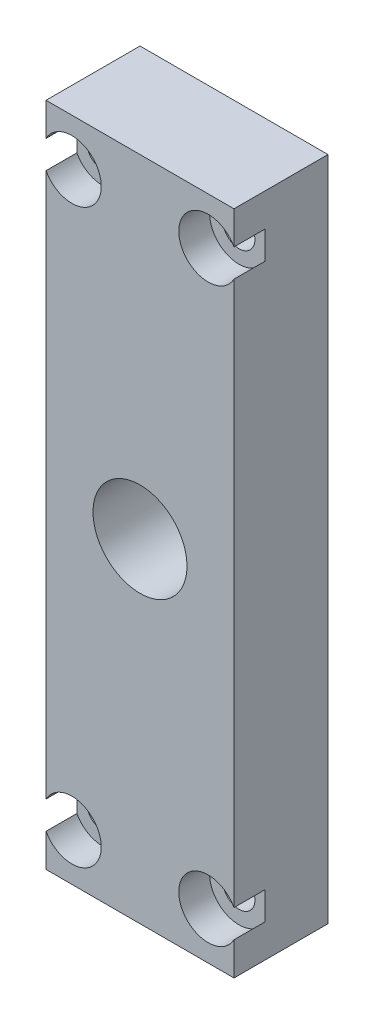
SolidWorks part; units mm, degrees
ref_plane "Front Plane" through (0, 0, 0) normal (0, 0, 1) x (1, 0, 0)
ref_plane "Top Plane" through (0, 0, 0) normal (0, 1, 0) x (1, 0, 0)
ref_plane "Right Plane" through (0, 0, 0) normal (1, 0, 0) x (0, 0, -1)
sketch "Sketch1" plane through (0, 0, 0) normal (0, 1, 0) x (1, 0, 0)
  line L1 (0, 0) -> (25.4, 0)
  line L2 (0, 0) -> (0, 12.7)
  line L3 (0, 12.7) -> (25.4, 12.7)
  line L4 (25.4, 0) -> (25.4, 12.7)
  dimension "D1" = 12.7
  dimension "D2" = 25.4
extrude "Boss-Extrude1" add sketch "Sketch1" along normal blind 90.0176
sketch "Sketch2" plane through (0, 0, 0) normal (0, 0, 1) x (1, 0, 0)
  line L0 (3.4925, 6.358) -> (21.9075, 6.358)
  line L1 (3.4925, 83.6676) -> (21.9075, 83.6676)
hole_wizard "CBORE for #8 Socket Head Cap Screw1" positions "3DSketch1" profile "Sketch4" counterbore size "#8" standard "ANSI Inch"
sketch3d "3DSketch1"
  point P0 (3.4925, 6.358, 0)
  point P3 (21.9075, 6.358, 0)
  point P6 (21.9075, 83.6676, 0)
  point P9 (3.4925, 83.6676, 0)
sketch "Sketch4" plane through (3.4925, 6.358, 0) normal (1, 0, 0) x (0, -1, 0)
  line L0 (0, 0) -> (0, 20.3434)
  line L1 (0, 20.3434) -> (2.1526, 19.05)
  line L2 (2.1526, 19.05) -> (2.1526, 4.1656)
  line L3 (2.1526, 4.1656) -> (3.9688, 4.1656)
  line L4 (3.9688, 4.1656) -> (3.9688, 0)
  line L5 (3.9688, 0) -> (0, 0)
  line L10 (0, 20.3434) -> (-2.1527, 19.05) construction
  line L11 (0, -6.35) -> (0, 107.95) construction
  dimension "Hole Dia." = 4.3053
  dimension "Hole Depth" = 19.05
  dimension "C'Bore Dia." = 7.9375
  dimension "C'Bore Depth" = 4.1656
  dimension "Drill Angle" = 118
sketch "Sketch5" plane through (0, 0, 0) normal (0, 0, 1) x (1, 0, 0)
  line L0 (12.7, 90.0176) -> (12.7, 0) construction
  line L1 (0, 90.0176) -> (25.4, 90.0176) construction
  line L2 (0, 0) -> (25.4, 0) construction
  line L3 (0, 45.0128) -> (25.4, 45.0128) construction
  line L4 (0, 81.7825) -> (0, 8.243) construction
  line L5 (25.4, 81.7825) -> (25.4, 8.243) construction
  point P12 (12.7, 45.0128)
  point P13 (12.7, 45.0128)
  point P14 (12.7, 45.0088)
hole_wizard "1/2 (0.5) Diameter Hole1" positions "3DSketch2" profile "Sketch6" hole size "1/2" standard "ANSI Inch"
sketch3d "3DSketch2"
  point P0 (12.7, 45.0128, 0)
sketch "Sketch6" plane through (12.7, 45.0128, 0) normal (1, 0, 0) x (0, -1, 0)
  line L0 (0, 0) -> (0, 19.0555)
  line L1 (0, 19.0555) -> (6.35, 15.24)
  line L2 (6.35, 15.24) -> (6.35, 0)
  line L5 (6.35, 0) -> (0, 0)
  line L10 (0, 19.0555) -> (-6.35, 15.24) construction
  line L11 (0, -6.35) -> (0, 107.95) construction
  dimension "Hole Dia." = 12.7
  dimension "Hole Depth" = 15.24
  dimension "Drill Angle" = 118
